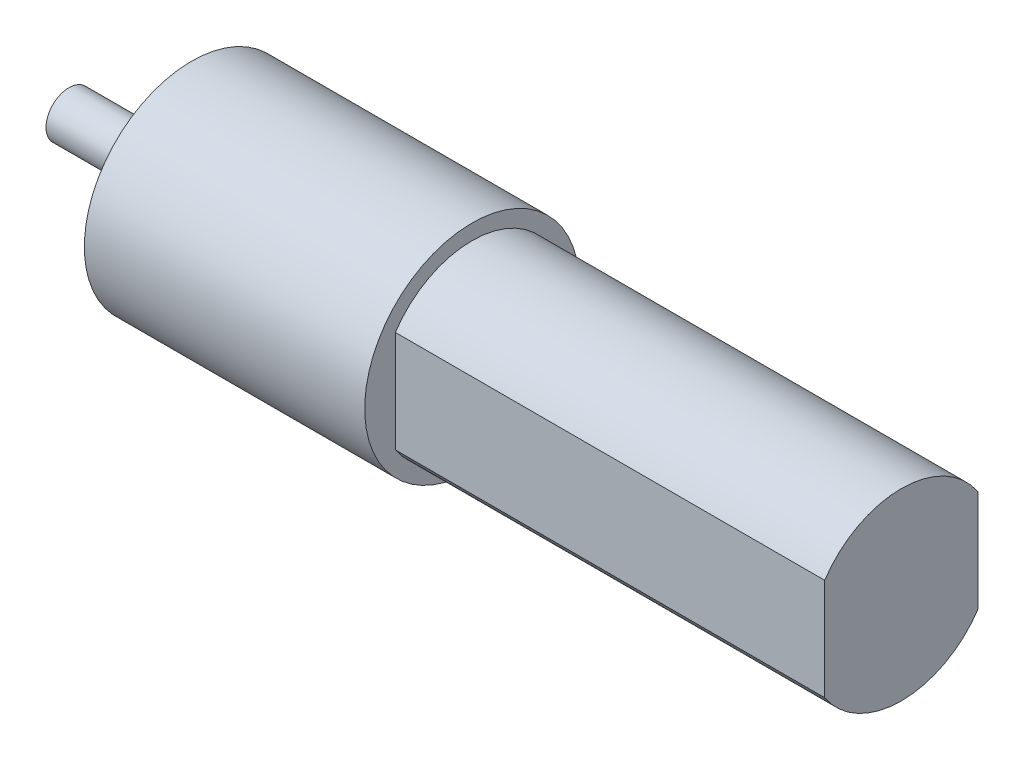
SolidWorks part; units mm, degrees
ref_plane "Front Plane" through (0, 0, 0) normal (0, 0, 1) x (1, 0, 0)
ref_plane "Top Plane" through (0, 0, 0) normal (0, 1, 0) x (1, 0, 0)
ref_plane "Right Plane" through (0, 0, 0) normal (1, 0, 0) x (0, 0, -1)
sketch "Sketch1" plane through (0, 0, 0) normal (1, 0, 0) x (0, 0, -1)
  circle A0 centre (0, 0) radius 11.1125
  dimension "D1" = 22.225
extrude "Boss-Extrude1" add sketch "Sketch1" along normal blind 29.0286
sketch "Sketch2" plane through (29.0286, 0, 0) normal (1, 0, 0) x (0, 0, -1)
  circle A0 centre (0, 0) radius 9.525
  dimension "D1" = 19.05
extrude "Boss-Extrude2" add sketch "Sketch2" along normal blind 44.45
sketch "Sketch3" plane through (73.4786, 0, 0) normal (1, 0, 0) x (0, 0, -1)
  line L0 (0, 9.525) -> (0, -9.525) construction
  line L1 (-7.9375, 0) -> (7.9375, 0) construction
  line L2 (-7.9375, 5.2651) -> (-7.9375, -5.2651)
  line L3 (-7.9375, -5.2651) -> (-10.4909, -5.2651)
  line L4 (-10.4909, -5.2651) -> (-10.4909, 5.2651)
  line L5 (-10.4909, 5.2651) -> (-7.9375, 5.2651)
  line L6 (7.9375, 5.2651) -> (7.9375, -5.2651)
  line L7 (7.9375, -5.2651) -> (10.6921, -5.2651)
  line L8 (10.6921, -5.2651) -> (10.6921, 5.2651)
  line L9 (10.6921, 5.2651) -> (7.9375, 5.2651)
  circle A0 centre (0, 0) radius 9.525 construction
  circle A1 centre (0, 0) radius 9.525 construction
  dimension "D1" = 15.875
  dimension "D3" = 7.9375
extrude "Cut-Extrude1" cut sketch "Sketch3" against normal blind 44.45
sketch "Sketch4" plane through (0, 0, 0) normal (-1, 0, 0) x (0, 0, 1)
  circle A0 centre (0, 0) radius 6.35
  dimension "D1" = 12.7
extrude "Boss-Extrude3" add sketch "Sketch4" along normal blind 1.5875
sketch "Sketch5" plane through (-1.5875, 0, 0) normal (-1, 0, 0) x (0, 0, 1)
  line L0 (0, 6.35) -> (0, -6.35) construction
  line L1 (-5.5562, 0) -> (5.5562, 0) construction
  line L2 (-5.5562, 3.0742) -> (-5.5562, -3.0742)
  line L3 (-5.5562, -3.0742) -> (-7.4155, -3.0742)
  line L4 (-7.4155, -3.0742) -> (-7.4155, 3.0742)
  line L5 (-7.4155, 3.0742) -> (-5.5562, 3.0742)
  line L6 (5.5562, 3.0742) -> (5.5562, -3.0742)
  line L7 (5.5562, -3.0742) -> (7.7891, -3.0742)
  line L8 (7.7891, -3.0742) -> (7.7891, 3.0742)
  line L9 (7.7891, 3.0742) -> (5.5562, 3.0742)
  circle A0 centre (0, 0) radius 6.35 construction
  circle A1 centre (0, 0) radius 6.35 construction
  dimension "D1" = 11.1125
extrude "Cut-Extrude2" cut sketch "Sketch5" against normal blind 1.5875
sketch "Sketch6" plane through (-1.5875, 0, 0) normal (-1, 0, 0) x (0, 0, 1)
  circle A0 centre (0, 0) radius 2.3813
  dimension "D1" = 4.7625
extrude "Boss-Extrude4" add sketch "Sketch6" along normal blind 11.1125
